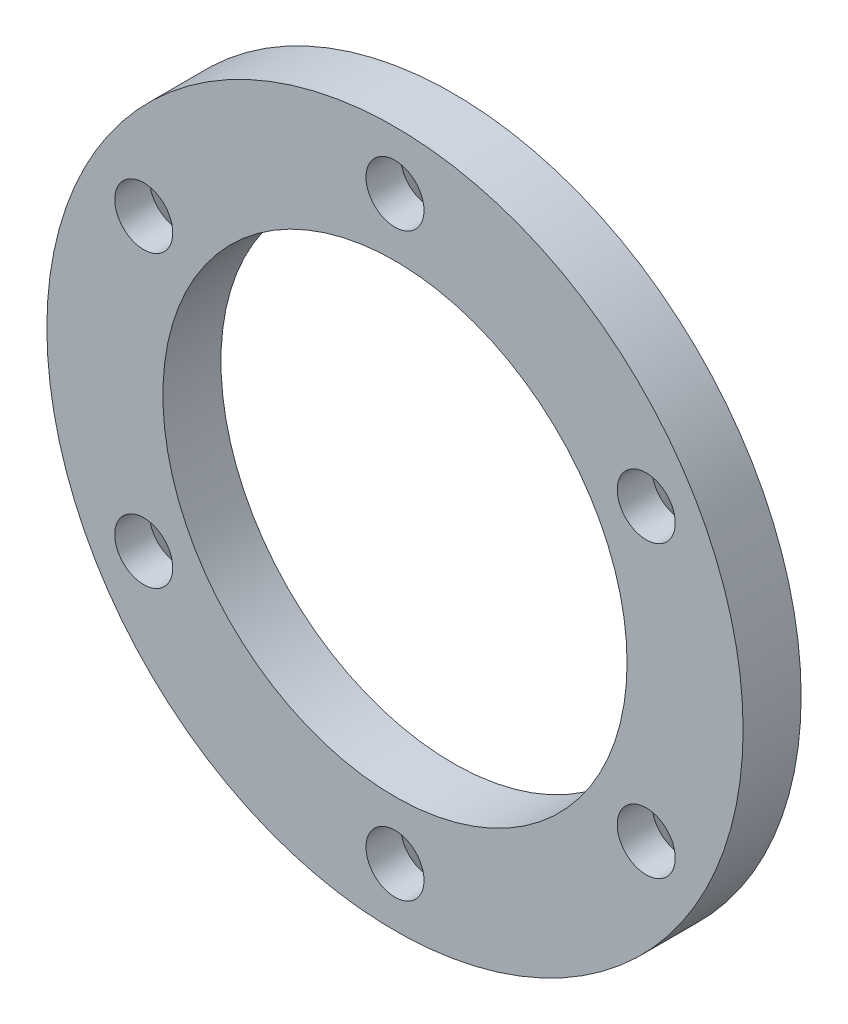
SolidWorks part; units mm, degrees
ref_plane "Front Plane" through (0, 0, 0) normal (0, 0, 1) x (1, 0, 0)
ref_plane "Top Plane" through (0, 0, 0) normal (0, 1, 0) x (1, 0, 0)
ref_plane "Right Plane" through (0, 0, 0) normal (1, 0, 0) x (0, 0, -1)
sketch "Sketch1" plane through (0, 0, 0) normal (0, 0, 1) x (1, 0, 0)
  line L0 (0, 0) -> (0, 25) construction
  line L5 (0, 0) -> (0, 7.7278) construction
  circle A9 centre (0, 0) radius 20
  circle A22 centre (0, 0) radius 30
  circle A23 centre (0, 25) radius 2.5
  circle A24 centre (21.6506, 12.5) radius 2.5
  circle A25 centre (21.6506, -12.5) radius 2.5
  circle A26 centre (0, -25) radius 2.5
  circle A27 centre (-21.6506, -12.5) radius 2.5
  circle A28 centre (-21.6506, 12.5) radius 2.5
  point P18 (0, 0)
  point P19 (0, 0)
  point P31 (0, 0)
  dimension "D1" = 25
  dimension "D2" = 5
  dimension "D3" = 60
  dimension "D4" = 6
  dimension "D5" = 40
extrude "Boss-Extrude1" add sketch "Sketch1" along normal blind 5
chamfer "Chamfer1" distance 2 angle 45 6 edges at (-19.1506, 12.5, 0) (-19.1506, -12.5, 0) (2.5, -25, 0) (24.1506, -12.5, 0) (24.1506, 12.5, 0) (2.5, 25, 0)
